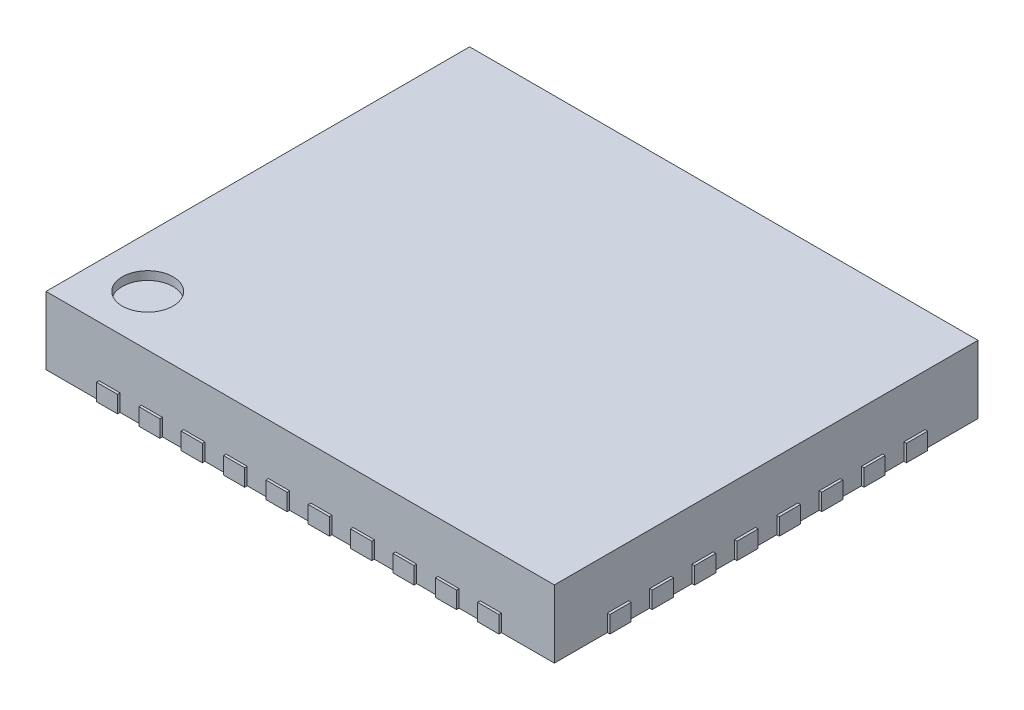
SolidWorks part; units mm, degrees
ref_plane "Front Plane" through (0, 0, 0) normal (0, 0, 1) x (1, 0, 0)
ref_plane "Top Plane" through (0, 0, 0) normal (0, 1, 0) x (1, 0, 0)
ref_plane "Right Plane" through (0, 0, 0) normal (1, 0, 0) x (0, 0, -1)
sketch "Sketch1" plane through (0, 0, 0) normal (0, 1, 0) x (1, 0, 0)
  line L0 (3, -2.5) -> (-3, 2.5) construction
  line L1 (-3, 2.5) -> (3, 2.5)
  line L2 (-3, 2.5) -> (-3, -2.5)
  line L3 (-3, -2.5) -> (3, -2.5)
  line L4 (3, 2.5) -> (3, -2.5)
  dimension "D1" = 6
  dimension "D2" = 5
extrude "Boss-Extrude1" add sketch "Sketch1" along normal blind 0.8
sketch "Sketch2" plane through (0, 0.8, 0) normal (0, 1, 0) x (1, 0, 0)
  line L0 (-3, -2.5) -> (3, -2.5) construction
  line L1 (-3, 2.5) -> (-3, -2.5) construction
  circle A0 centre (-2.4, -1.9) radius 0.3
  dimension "D1" = 0.6
  dimension "D3" = 0.6
  dimension "D2" = 0.6
extrude "Cut-Extrude1" cut sketch "Sketch2" against normal blind 0.1
sketch "Sketch3" plane through (0, 0, 2.5) normal (0, 0, 1) x (1, 0, 0)
  line L0 (-3, 0) -> (3, 0) construction
  line L1 (-0.375, 0) -> (-0.125, 0)
  line L2 (-0.375, 0) -> (-0.375, 0.2)
  line L3 (-0.375, 0.2) -> (-0.125, 0.2)
  line L4 (-0.125, 0) -> (-0.125, 0.2)
  line L5 (-0.25, 0.2) -> (-0.25, 0.9938) construction
  line L6 (0.375, 0) -> (0.375, 0.2)
  line L7 (0.125, 0) -> (0.375, 0)
  line L8 (0.125, 0) -> (0.125, 0.2)
  line L9 (0.125, 0.2) -> (0.375, 0.2)
  line L10 (0.875, 0) -> (0.875, 0.2)
  line L11 (0.625, 0) -> (0.875, 0)
  line L12 (0.625, 0) -> (0.625, 0.2)
  line L13 (0.625, 0.2) -> (0.875, 0.2)
  line L14 (1.375, 0) -> (1.375, 0.2)
  line L15 (1.125, 0) -> (1.375, 0)
  line L16 (1.125, 0) -> (1.125, 0.2)
  line L17 (1.125, 0.2) -> (1.375, 0.2)
  line L18 (1.875, 0) -> (1.875, 0.2)
  line L19 (1.625, 0) -> (1.875, 0)
  line L20 (1.625, 0) -> (1.625, 0.2)
  line L21 (1.625, 0.2) -> (1.875, 0.2)
  line L22 (2.375, 0) -> (2.375, 0.2)
  line L23 (2.125, 0) -> (2.375, 0)
  line L24 (2.125, 0) -> (2.125, 0.2)
  line L25 (2.125, 0.2) -> (2.375, 0.2)
  line L26 (-0.875, 0) -> (-0.625, 0)
  line L27 (-0.875, 0) -> (-0.875, 0.2)
  line L28 (-0.875, 0.2) -> (-0.625, 0.2)
  line L29 (-0.625, 0) -> (-0.625, 0.2)
  line L30 (-1.375, 0) -> (-1.125, 0)
  line L31 (-1.375, 0) -> (-1.375, 0.2)
  line L32 (-1.375, 0.2) -> (-1.125, 0.2)
  line L33 (-1.125, 0) -> (-1.125, 0.2)
  line L34 (-1.875, 0) -> (-1.625, 0)
  line L35 (-1.875, 0) -> (-1.875, 0.2)
  line L36 (-1.875, 0.2) -> (-1.625, 0.2)
  line L37 (-1.625, 0) -> (-1.625, 0.2)
  line L38 (-2.375, 0) -> (-2.125, 0)
  line L39 (-2.375, 0) -> (-2.375, 0.2)
  line L40 (-2.375, 0.2) -> (-2.125, 0.2)
  line L41 (-2.125, 0) -> (-2.125, 0.2)
  dimension "D1" = 0.25
  dimension "D2" = 0.25
  dimension "D3" = 0.2
  dimension "D4" = 6
  dimension "D5" = 5
extrude "Boss-Extrude2" add sketch "Sketch3" along normal blind 0.03
pattern_linear "LPattern1" count 2 spacing 5.03 along (0, 0, -1) of "Boss-Extrude2"
sketch "Sketch4" plane through (3, 0, 0) normal (1, 0, 0) x (0, 0, -1)
  line L0 (-2.5, 0) -> (2.5, 0) construction
  line L1 (-0.375, 0) -> (-0.125, 0)
  line L2 (-0.375, 0) -> (-0.375, 0.2)
  line L3 (-0.375, 0.2) -> (-0.125, 0.2)
  line L4 (-0.125, 0) -> (-0.125, 0.2)
  line L5 (-0.25, 0.2) -> (-0.25, 0.8593) construction
  line L6 (0.125, 0.2) -> (0.375, 0.2)
  line L7 (0.125, 0) -> (0.125, 0.2)
  line L8 (0.125, 0) -> (0.375, 0)
  line L9 (0.375, 0) -> (0.375, 0.2)
  line L10 (0.625, 0.2) -> (0.875, 0.2)
  line L11 (0.625, 0) -> (0.625, 0.2)
  line L12 (0.625, 0) -> (0.875, 0)
  line L13 (0.875, 0) -> (0.875, 0.2)
  line L14 (1.125, 0.2) -> (1.375, 0.2)
  line L15 (1.125, 0) -> (1.125, 0.2)
  line L16 (1.125, 0) -> (1.375, 0)
  line L17 (1.375, 0) -> (1.375, 0.2)
  line L18 (1.625, 0.2) -> (1.875, 0.2)
  line L19 (1.625, 0) -> (1.625, 0.2)
  line L20 (1.625, 0) -> (1.875, 0)
  line L21 (1.875, 0) -> (1.875, 0.2)
  line L22 (-0.875, 0.2) -> (-0.625, 0.2)
  line L23 (-0.875, 0) -> (-0.875, 0.2)
  line L24 (-0.875, 0) -> (-0.625, 0)
  line L25 (-0.625, 0) -> (-0.625, 0.2)
  line L26 (-1.375, 0.2) -> (-1.125, 0.2)
  line L27 (-1.375, 0) -> (-1.375, 0.2)
  line L28 (-1.375, 0) -> (-1.125, 0)
  line L29 (-1.125, 0) -> (-1.125, 0.2)
  line L30 (-1.875, 0.2) -> (-1.625, 0.2)
  line L31 (-1.875, 0) -> (-1.875, 0.2)
  line L32 (-1.875, 0) -> (-1.625, 0)
  line L33 (-1.625, 0) -> (-1.625, 0.2)
  dimension "D1" = 0.25
  dimension "D2" = 0.25
  dimension "D3" = 5
  dimension "D4" = 4
extrude "Boss-Extrude3" add sketch "Sketch4" along normal blind 0.03
pattern_linear "LPattern2" count 2 spacing 6.03 along (-1, 0, 0) of "Boss-Extrude3"
